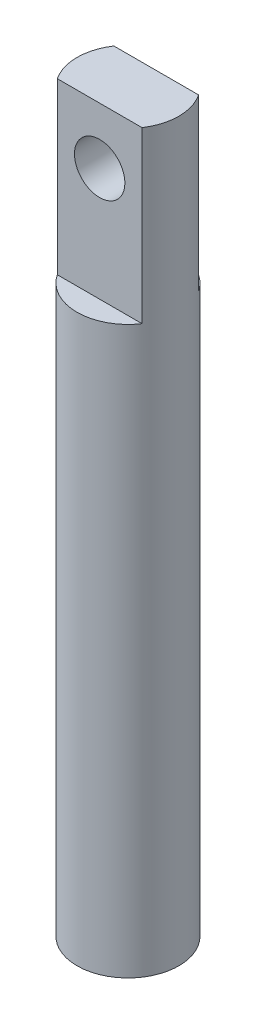
SolidWorks part; units mm, degrees
material "Chrome Stainless Steel"
ref_plane "Front Plane" through (0, 0, 0) normal (0, 0, 1) x (1, 0, 0)
ref_plane "Top Plane" through (0, 0, 0) normal (0, 1, 0) x (1, 0, 0)
ref_plane "Right Plane" through (0, 0, 0) normal (1, 0, 0) x (0, 0, -1)
sketch "Sketch1" plane through (0, 0, 0) normal (0, 1, 0) x (1, 0, 0)
  circle A0 centre (0, 0) radius 2.286
  dimension "D1" = 4.572
extrude "Extrude1" add sketch "Sketch1" along normal blind 25.4
sketch "Sketch2" plane through (0, 25.4, 0) normal (0, 1, 0) x (-1, 0, 0)
  line L0 (2.286, 0) -> (-2.286, 0) construction
  line L1 (2.286, -1.27) -> (-2.286, -1.27)
  line L2 (2.286, -1.27) -> (2.286, 1.27)
  line L3 (2.286, 1.27) -> (-2.286, 1.27)
  line L4 (-2.286, -1.27) -> (-2.286, 1.27)
  line L6 (0, -1.27) -> (0, 1.27) construction
  circle A0 centre (0, 0) radius 2.286 construction
  dimension "D1" = 2.54
  dimension "D2" = 4.572
extrude "Extrude2" add sketch "Sketch2" along normal blind 7.62
sketch "Sketch3" plane through (0, 25.4, 0) normal (0, 1, 0) x (-1, 0, 0)
  circle A0 centre (0, 0) radius 2.286
extrude "Cut-Extrude1" cut sketch "Sketch3" along normal blind 7.62 flip side to cut
hole_wizard "Tap Drill for #4 Tap1" positions "3DSketch1" profile "Sketch4" hole size "#4-40" standard "Ansi Inch"
sketch3d "3DSketch1"
  line L0 (1.9008, 33.02, -1.27) -> (-1.9008, 33.02, -1.27) construction
  line L1 (1.9008, 33.02, -1.27) -> (1.9008, 25.4, -1.27) construction
  line L2 (-1.9008, 25.4, -1.27) -> (-1.9008, 33.02, -1.27) construction
  point P0 (0, 30.48, -1.27)
  dimension "D1" = 2.54
  dimension "D2" = 1.9008
  dimension "D3" = 1.9008
sketch "Sketch4" plane through (0, 30.48, -1.27) normal (1, 0, 0) x (0, 1, 0)
  line L0 (0, 0) -> (0, 7.0292)
  line L1 (0, 7.0292) -> (1.1303, 6.35)
  line L2 (1.1303, 6.35) -> (1.1303, 0)
  line L5 (1.1303, 0) -> (0, 0)
  line L10 (0, 7.0292) -> (-1.1303, 6.35) construction
  line L11 (0, -6.35) -> (0, 107.95) construction
  dimension "Hole Dia." = 2.2606
  dimension "Hole Depth" = 6.35
  dimension "Drill Angle" = 118
